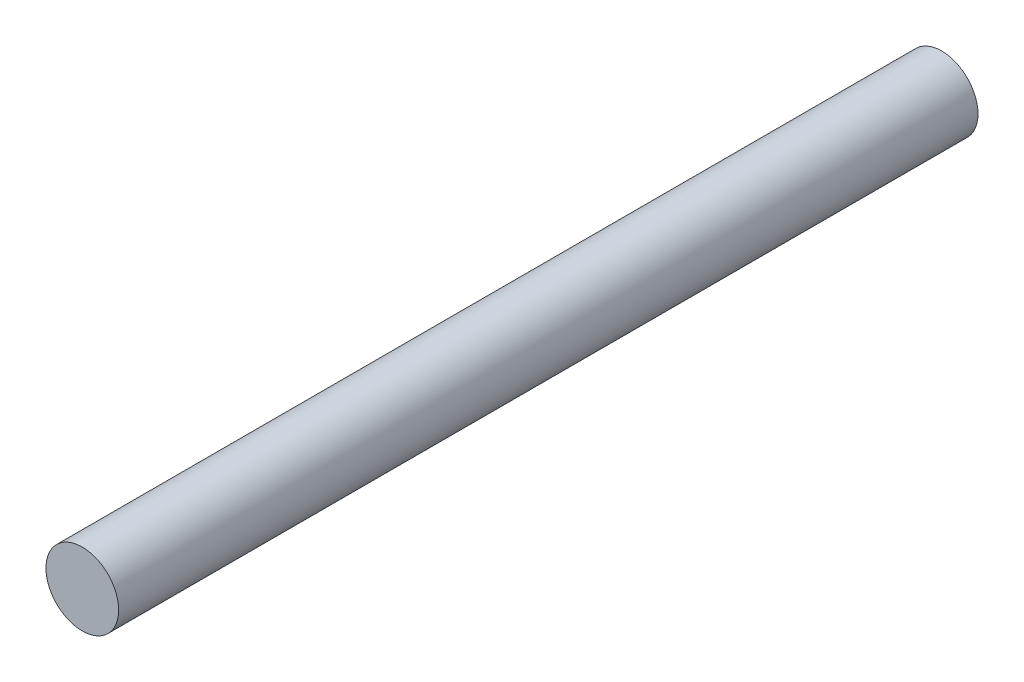
SolidWorks part; units mm, degrees
ref_plane "Front Plane" through (0, 0, 0) normal (0, 0, 1) x (1, 0, 0)
ref_plane "Top Plane" through (0, 0, 0) normal (0, 1, 0) x (1, 0, 0)
ref_plane "Right Plane" through (0, 0, 0) normal (1, 0, 0) x (0, 0, -1)
sketch "Sketch1" plane through (0, 0, 0) normal (0, 0, 1) x (1, 0, 0)
  circle A0 centre (-2.6785, -4.2187) radius 5.5
  dimension "D1" = 11
extrude "Boss-Extrude1" add sketch "Sketch1" along normal blind 130
